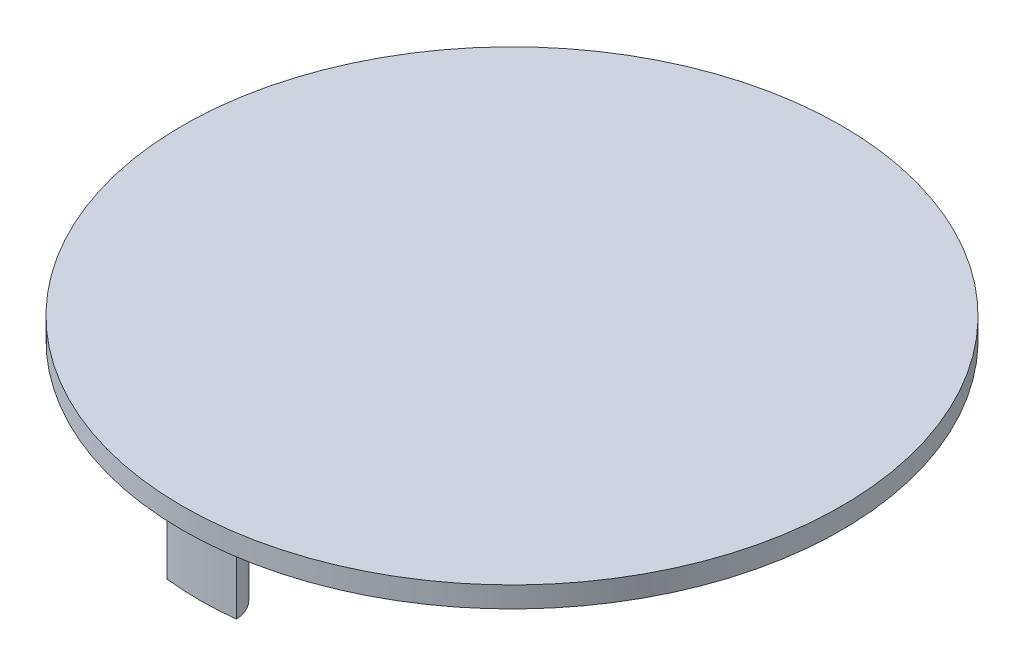
SolidWorks part; units mm, degrees
ref_plane "Front Plane" through (0, 0, 0) normal (0, 0, 1) x (1, 0, 0)
ref_plane "Top Plane" through (0, 0, 0) normal (0, 1, 0) x (1, 0, 0)
ref_plane "Right Plane" through (0, 0, 0) normal (1, 0, 0) x (0, 0, -1)
sketch "Sketch2" plane through (0, 0, 0) normal (0, 1, 0) x (1, 0, 0)
  circle A0 centre (0, 0) radius 47.5
  dimension "D1" = 95
extrude "Boss-Extrude1" add sketch "Sketch2" along normal blind 3
sketch "Sketch4" plane through (0, 0, 0) normal (0, -1, 0) x (1, 0, 0)
  arc A2 (4.9923, 44.7222) -> (-4.9923, 44.7222) centre (0, 0) ccw
  arc A3 (-4.9923, 44.7222) -> (4.9923, 44.7222) centre (0, 45) ccw
  dimension "D1" = 10
  dimension "D2" = 90
extrude "Boss-Extrude2" add sketch "Sketch4" along normal blind 10
